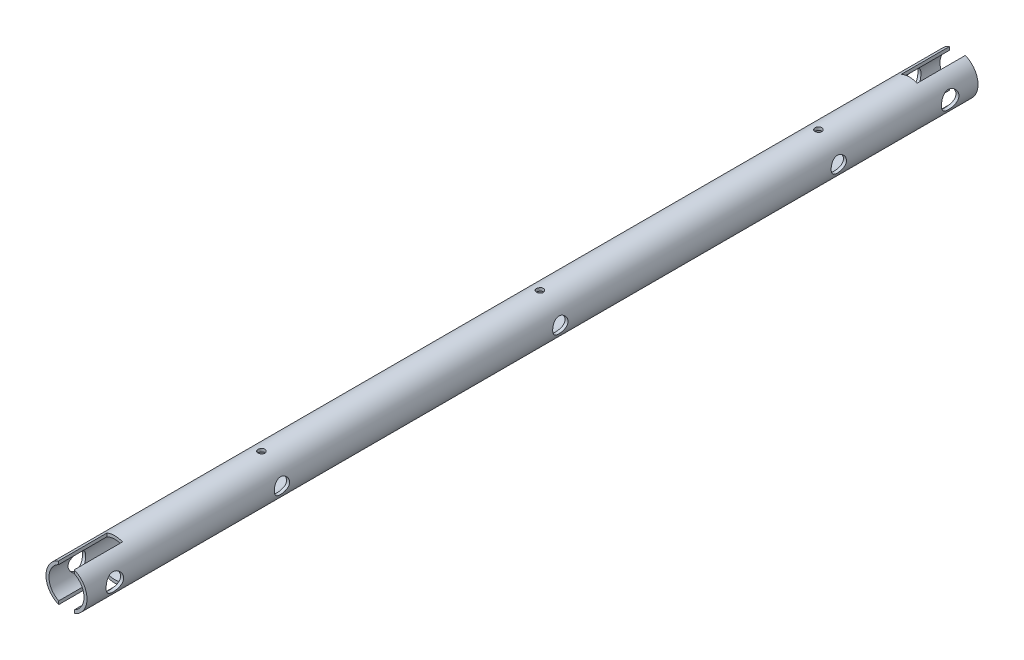
SolidWorks part; units mm, degrees
ref_plane "Front" through (0, 0, 0) normal (0, 0, 1) x (1, 0, 0)
ref_plane "Top" through (0, 0, 0) normal (0, 1, 0) x (1, 0, 0)
ref_plane "Right" through (0, 0, 0) normal (1, 0, 0) x (0, 0, -1)
sketch "Sketch1" plane through (0, 0, 0) normal (0, 0, 1) x (1, 0, 0)
  circle A0 centre (0, 0) radius 9.36
  circle A1 centre (0, 0) radius 7.99
extrude "Extrude1" add sketch "Sketch1" along normal blind 406.4
sketch "Sketch2" plane through (0, 0, 0) normal (1, 0, 0) x (0, 0, -1)
  line L0 (-406.4, 0) -> (0, 0) construction
  line L1 (0, -9.36) -> (0, 9.36) construction
  circle A0 centre (-12.7, 0) radius 4
  dimension "D1" = 8
  dimension "D2" = 12.7
extrude "Cut-Extrude1" cut sketch "Sketch2" along normal through all and the other way through all
sketch "Sketch4" plane through (0, 0, 0) normal (1, 0, 0) x (0, 0, -1)
  line L0 (-406.4, 0) -> (0, 0) construction
  circle A0 centre (-393.7, 0) radius 4
extrude "Cut-Extrude4" cut sketch "Sketch4" against normal through all and the other way through all
sketch "Sketch5" plane through (0, 0, 0) normal (0, 1, 0) x (1, 0, 0)
  line L0 (7.99, 0) -> (-7.99, 0) construction
  line L1 (-3.57, 0) -> (3.57, 0)
  line L2 (-3.57, 0) -> (-3.57, -22)
  line L3 (-3.57, -22) -> (3.57, -22)
  line L4 (3.57, 0) -> (3.57, -22)
extrude "Cut-Extrude5" cut sketch "Sketch5" against normal through all and the other way through all
sketch "Sketch6" plane through (0, 0, 0) normal (0, 1, 0) x (1, 0, 0)
  line L1 (-3.55, -406.4) -> (3.55, -406.4)
  line L2 (-3.55, -406.4) -> (-3.55, -384.4)
  line L3 (-3.55, -384.4) -> (3.55, -384.4)
  line L4 (3.55, -406.4) -> (3.55, -384.4)
  line L5 (-9.36, -406.4) -> (9.36, -406.4) construction
extrude "Cut-Extrude6" cut sketch "Sketch6" against normal through all and the other way through all
sketch "Sketch7" plane through (0, 0, 0) normal (1, 0, 0) x (0, 0, -1)
  line L0 (-406.4, 0) -> (-384.4, 0) construction
  circle A0 centre (-63.5, 0) radius 3.5
extrude "Cut-Extrude7" cut sketch "Sketch7" along normal through all
sketch "Sketch8" plane through (0, 0, 0) normal (1, 0, 0) x (0, 0, -1)
  circle A0 centre (-190.5, 0) radius 3.5
extrude "Cut-Extrude9" cut sketch "Sketch8" along normal through all
sketch "Sketch9" plane through (0, 0, 0) normal (1, 0, 0) x (0, 0, -1)
  line L0 (-406.4, 0) -> (-384.4, 0) construction
  circle A0 centre (-317.5, 0) radius 3.5
extrude "Cut-Extrude10" cut sketch "Sketch9" along normal through all
sketch "Sketch10" plane through (0, 0, 0) normal (0, 1, 0) x (1, 0, 0)
  line L0 (0, -22) -> (0, 0) construction
  circle A0 centre (0, -63.5) radius 1.55
extrude "Cut-Extrude11" cut sketch "Sketch10" against normal through all and the other way through all
sketch "Sketch11" plane through (0, 0, 0) normal (0, 1, 0) x (1, 0, 0)
  line L0 (0, -22) -> (0, 0) construction
  circle A0 centre (0, -190.5) radius 1.55
extrude "Cut-Extrude12" cut sketch "Sketch11" against normal through all and the other way through all
sketch "Sketch12" plane through (0, 0, 0) normal (0, 1, 0) x (1, 0, 0)
  line L0 (0, -22) -> (0, 0) construction
  circle A0 centre (0, -317.5) radius 1.55
extrude "Cut-Extrude13" cut sketch "Sketch12" against normal through all and the other way through all
